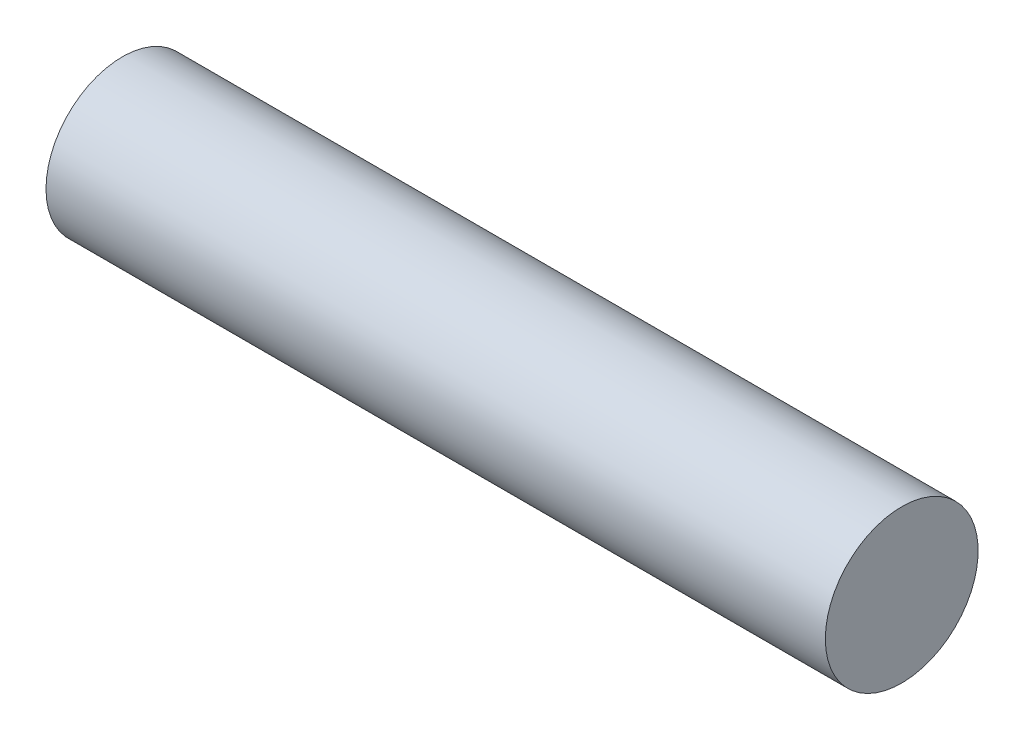
SolidWorks part; units mm, degrees
ref_plane "Front Plane" through (0, 0, 0) normal (0, 0, 1) x (1, 0, 0)
ref_plane "Top Plane" through (0, 0, 0) normal (0, 1, 0) x (1, 0, 0)
ref_plane "Right Plane" through (0, 0, 0) normal (1, 0, 0) x (0, 0, -1)
sketch "Sketch1" plane through (0, 0, 0) normal (0, 0, 1) x (1, 0, 0)
  line L1 (0, 0) -> (765, 0)
  line L2 (0, 0) -> (0, 75)
  line L3 (0, 75) -> (765, 75)
  line L4 (765, 0) -> (765, 75)
  dimension "D1" = 765
  dimension "D2" = 75
revolve "Revolve1" add sketch "Sketch1" angle 360 about L1
